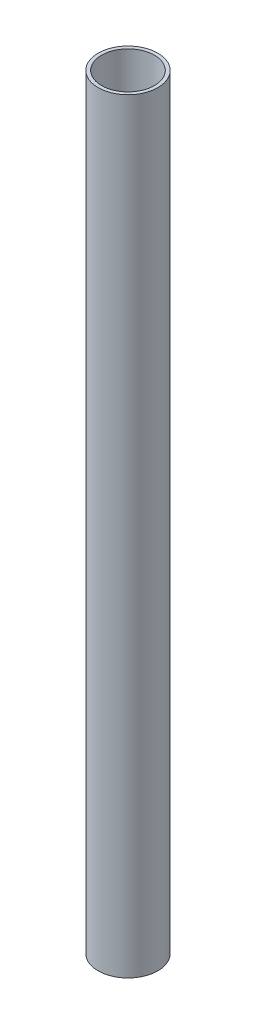
SolidWorks part; units mm, degrees
ref_plane "前视基准面" through (0, 0, 0) normal (0, 0, 1) x (1, 0, 0)
ref_plane "上视基准面" through (0, 0, 0) normal (0, 1, 0) x (1, 0, 0)
ref_plane "右视基准面" through (0, 0, 0) normal (1, 0, 0) x (0, 0, -1)
sketch "草图1" plane through (0, 0, 0) normal (0, 1, 0) x (1, 0, 0)
  circle A0 centre (0, 0) radius 13
  circle A1 centre (0, 0) radius 11.5
  dimension "D1" = 26
  dimension "D2" = 23
extrude "凸台-拉伸1" add sketch "草图1" along normal blind 333
